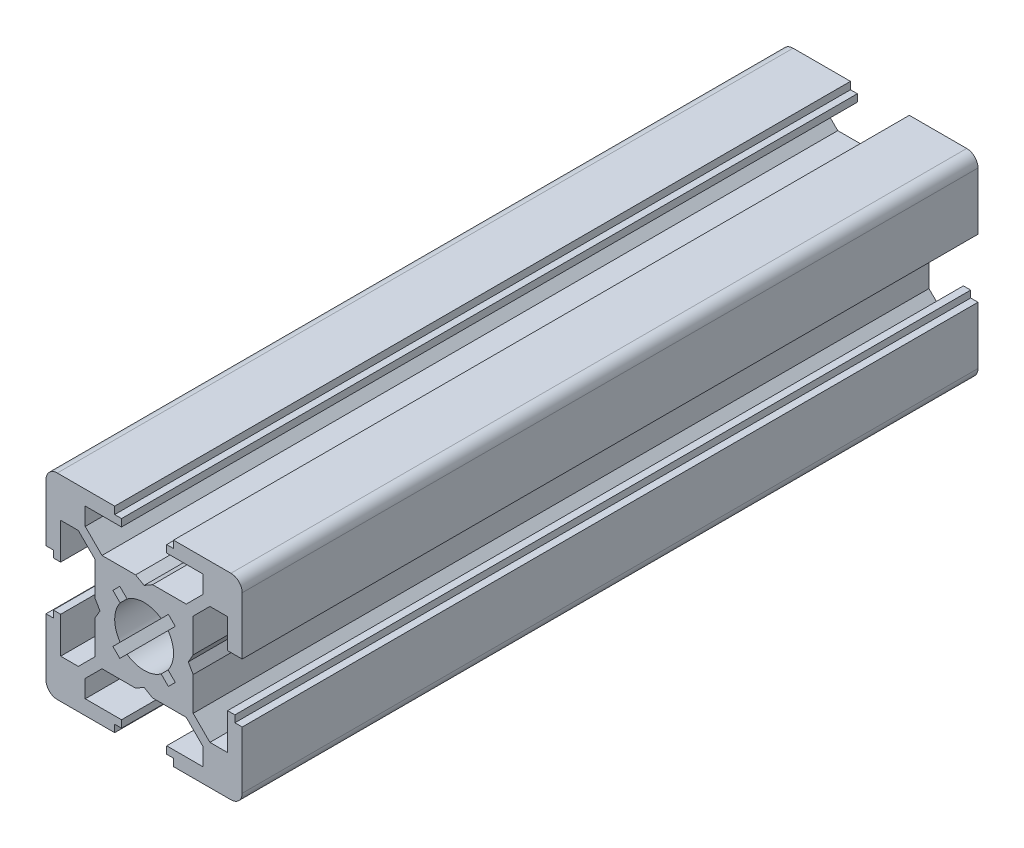
SolidWorks part; units mm, degrees
material "Aleación 1060"
ref_plane "Plano frontal" through (0, 0, 0) normal (0, 0, 1) x (1, 0, 0)
ref_plane "Plano superior" through (0, 0, 0) normal (0, 1, 0) x (1, 0, 0)
ref_plane "Plano direito" through (0, 0, 0) normal (1, 0, 0) x (0, 0, -1)
sketch "Esboço1" plane through (0, 0, 0) normal (0, 0, 1) x (1, 0, 0)
  line L0 (-6, -6.7071) -> (-4.2929, -5)
  line L1 (-8.85, 10) -> (-3, 10)
  line L2 (-10, 8.85) -> (-10, 3)
  line L3 (-8.85, -10) -> (-3, -10)
  line L4 (10, 8.85) -> (10, 3)
  line L5 (-10, 10) -> (10, -10) construction
  line L6 (-10, -10) -> (8.5078, 8.5078) construction
  line L7 (-8.5078, -2.3) -> (-8.5078, -6)
  line L8 (-6.7071, 6) -> (-5, 4.2929)
  line L9 (-6, 6.7071) -> (-4.2929, 5)
  line L11 (8.5078, 6) -> (8.5078, 2.3)
  line L12 (-6.7071, -6) -> (-5, -4.2929)
  line L13 (-8.5078, 6) -> (-8.5078, 2.3)
  line L14 (8.5078, 3) -> (10, 3)
  line L15 (9.2539, -3) -> (10, -3)
  line L16 (3, 10) -> (3, 9.2539)
  line L17 (-3, 10) -> (-3, 9.2539)
  line L18 (-9.2539, 3) -> (-10, 3)
  line L19 (-9.2539, -3) -> (-10, -3)
  line L20 (2.3, 8.5078) -> (6, 8.5078)
  line L21 (10, -3) -> (10, -8.85)
  line L22 (-3.182, 2.4749) -> (-2.4749, 3.182)
  line L23 (-4.2929, 5) -> (-0.866, 5)
  line L24 (-5, 4.2929) -> (-5, 0.866)
  line L25 (-4.2929, -5) -> (-0.866, -5)
  line L26 (5, 4.2929) -> (5, 0.866)
  line L27 (-6, 5) -> (-5, 4.1667) construction
  line L28 (0.866, 5) -> (0, 4.5021)
  line L29 (2.4749, 3.182) -> (3.182, 2.4749)
  line L30 (3.182, -2.4749) -> (2.4749, -3.182)
  line L31 (-3.182, -2.4749) -> (-2.4749, -3.182)
  line L32 (-2.4749, 3.182) -> (-1.7381, 2.4452)
  line L33 (1.7381, 2.4452) -> (2.4749, 3.182)
  line L34 (-9.6464, 10.3536) -> (10.3536, -9.6464) construction
  line L35 (2.4452, 1.7381) -> (3.182, 2.4749)
  line L36 (-10, -3) -> (-10, -8.85)
  line L37 (2.4452, -1.7381) -> (3.182, -2.4749)
  line L38 (-9.6464, -10.3536) -> (10.3536, 9.6464) construction
  line L39 (1.7381, -2.4452) -> (2.4749, -3.182)
  line L40 (-3.182, 2.4749) -> (-2.4452, 1.7381)
  line L41 (-10.3536, 9.6464) -> (9.6464, -10.3536) construction
  line L42 (-3.182, -2.4749) -> (-2.4452, -1.7381)
  line L43 (-2.4749, -3.182) -> (-1.7381, -2.4452)
  line L44 (4.2929, -5) -> (6, -6.7071)
  line L45 (5, -4.2929) -> (6.7071, -6)
  line L46 (5, 4.2929) -> (6.7071, 6)
  line L47 (4.2929, 5) -> (6, 6.7071)
  line L48 (0.866, 5) -> (4.2929, 5)
  line L50 (4.5027, 0) -> (5, 0.866)
  line L51 (5, -0.8677) -> (4.5027, 0)
  line L52 (0.866, -5) -> (4.2929, -5)
  line L53 (-4.4981, -0.0008) -> (-5, 0.866)
  line L54 (-4.4981, -0.0008) -> (-5, -0.8677)
  line L55 (9.2539, 3) -> (9.2539, 2.3)
  line L56 (0, -4.5) -> (0.866, -5)
  line L57 (0, -4.5) -> (-0.866, -5)
  line L58 (-5, -0.8677) -> (-5, -4.2929)
  line L61 (5, -0.8677) -> (5, -4.2929)
  line L62 (9.2539, 2.3) -> (8.5078, 2.3)
  line L63 (9.2539, -3) -> (9.2539, -2.3)
  line L64 (9.2539, -2.3) -> (8.5078, -2.3)
  line L65 (-3, 9.2539) -> (-2.3, 9.2539)
  line L66 (-2.3, 9.2539) -> (-2.3, 8.5078)
  line L67 (3, 9.2539) -> (2.3, 9.2539)
  line L68 (2.3, 9.2539) -> (2.3, 8.5078)
  line L69 (-6, 8.5078) -> (-2.3, 8.5078)
  line L71 (6, 8.5078) -> (6, 6.7071)
  line L72 (8.5078, 6) -> (6.7071, 6)
  line L73 (-6, 8.5078) -> (-6, 6.7071)
  line L74 (-8.5078, 6) -> (-6.7071, 6)
  line L75 (-0.866, 5) -> (0, 4.5021)
  line L76 (8.5078, -2.3) -> (8.5078, -6)
  line L77 (-8.5078, -6) -> (-6.7071, -6)
  line L78 (-9.2539, -3) -> (-9.2539, -2.3)
  line L79 (-9.2539, -2.3) -> (-8.5078, -2.3)
  line L80 (-9.2539, 3) -> (-9.2539, 2.3)
  line L81 (-9.2539, 2.3) -> (-8.5078, 2.3)
  line L82 (-3, -9.2539) -> (-3, -10)
  line L83 (3, -9.2539) -> (3, -10)
  line L84 (-6, -8.5078) -> (-2.3, -8.5078)
  line L85 (8.5078, 8.5078) -> (8.5078, -8.5078) construction
  line L86 (-3, -9.2539) -> (-2.3, -9.2539)
  line L87 (-2.3, -9.2539) -> (-2.3, -8.5078)
  line L88 (3, -9.2539) -> (2.3, -9.2539)
  line L89 (2.3, -9.2539) -> (2.3, -8.5078)
  line L90 (-6, -8.5078) -> (-6, -6.7071)
  line L91 (6, -8.5078) -> (6, -6.7071)
  line L92 (8.5078, -6) -> (6.7071, -6)
  line L93 (3, -10) -> (8.85, -10)
  line L94 (2.3, -8.5078) -> (6, -8.5078)
  line L95 (-10, -10) -> (10, -10) construction
  line L96 (-8.5078, 8.5078) -> (-8.5078, -8.5078) construction
  line L97 (-8.5078, -8.5078) -> (8.5078, -8.5078) construction
  line L98 (-10, 10) -> (-10, -10) construction
  line L99 (10, 10) -> (10, -10) construction
  line L100 (-10, -10) -> (10, 10) construction
  line L101 (3, 10) -> (8.85, 10)
  line L102 (-8.5078, 8.5078) -> (8.5078, 8.5078) construction
  line L104 (-10, 10) -> (10, 10) construction
  arc A0 (1.7381, 2.4452) -> (-1.7381, 2.4452) centre (0, 0) ccw
  arc A1 (2.4452, -1.7381) -> (2.4452, 1.7381) centre (0, 0) ccw
  arc A2 (-1.7381, -2.4452) -> (1.7381, -2.4452) centre (0, 0) ccw
  arc A3 (-2.4452, 1.7381) -> (-2.4452, -1.7381) centre (0, 0) ccw
  arc A4 (-10, -8.85) -> (-8.85, -10) centre (-8.85, -8.85) ccw
  arc A5 (8.85, -10) -> (10, -8.85) centre (8.85, -8.85) ccw
  arc A6 (8.85, 10) -> (10, 8.85) centre (8.85, 8.85) cw
  arc A7 (-10, 8.85) -> (-8.85, 10) centre (-8.85, 8.85) cw
  point P0 (0, 0)
  point P10 (-10.3536, -9.6464)
  point P11 (9.6464, 10.3536)
  point P64 (0, 4.7929)
  point P65 (0, -5)
  point P66 (5, 0)
  point P67 (-5, 0)
  dimension "D1" = 1.15
extrude "Ressalto-extrusão1" add sketch "Esboço1" along normal mid plane 75 contours A7 L2 L18 L80 L81 L13 L74 L8 L24 L53 L54 L58 L12 L77 L7 L79 L78 L19 L36 A4 L3 L82 L86 L87 L84 L90 L0 L25 L57 L56 L52 L44 L91 L94 L89 L88 L83 L93 A5 L21 L15 L63 L64 L76 L92 L45 L61 L51 L50 L26 L46
sketch "Croquis1" plane through (0, 0, 0) normal (1, 0, 0) x (0, 0, -1)
  line L0 (0, 0) -> (-27.5, 0) construction
  line L2 (37.5, 8.85) -> (37.5, 3) construction
  circle A0 centre (-27.5, 0) radius 3
  dimension "D1" = 6
  dimension "D2" = 65
